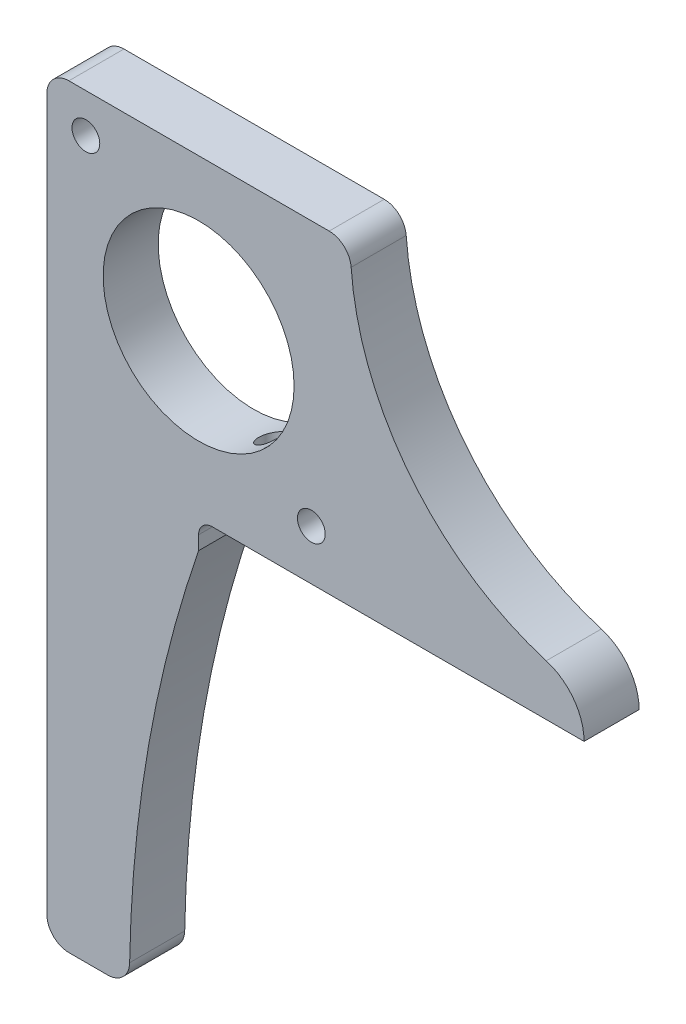
SolidWorks part; units mm, degrees
ref_plane "Front Plane" through (0, 0, 0) normal (0, 0, 1) x (1, 0, 0)
ref_plane "Top Plane" through (0, 0, 0) normal (0, 1, 0) x (1, 0, 0)
ref_plane "Right Plane" through (0, 0, 0) normal (1, 0, 0) x (0, 0, -1)
sketch "Sketch1" plane through (0, 0, 0) normal (0, 0, 1) x (1, 0, 0)
  line L0 (0, 0) -> (35, 0)
  line L1 (61.95, -36.27) -> (61.95, -43.3792) construction
  line L2 (9.525, -87.07) -> (0, -87.07)
  line L3 (0, -36.27) -> (0, 0)
  line L4 (30.5, -30.5) -> (4.5, -4.5) construction
  line L5 (4.5, -4.5) -> (30.5, -4.5) construction
  line L6 (4.5, -4.5) -> (4.5, -30.5) construction
  line L7 (4.5, -30.5) -> (30.5, -30.5) construction
  line L8 (30.5, -4.5) -> (30.5, -30.5) construction
  line L9 (0, -36.27) -> (35, -36.27) construction
  line L10 (35, -36.27) -> (35, 0) construction
  line L11 (4.5, -30.5) -> (30.5, -4.5) construction
  line L12 (9.525, -87.07) -> (9.525, -96.7126) construction
  line L13 (0, -87.07) -> (0, -36.27)
  line L14 (17.5, -36.27) -> (61.95, -36.27)
  line L15 (17.5, -36.27) -> (17.5, -39.445)
  line L16 (17.5, -39.445) -> (17.5, -17.5) construction
  arc A0 (9.525, -87.07) -> (17.5, -39.445) centre (155.7157, -87.07) cw
  arc A1 (35, 0) -> (57.5878, -30.3993) centre (66.75, 0) ccw
  circle A2 centre (4.5, -4.5) radius 1.6002
  circle A3 centre (17.5, -17.5) radius 11.0109
  circle A4 centre (30.5, -30.5) radius 1.6002
  arc A5 (61.95, -36.27) -> (57.5878, -30.3993) centre (55.8185, -36.27) ccw
  point P17 (17.5, -17.5)
  dimension "D3" = 3.2004
  dimension "D4" = 36.27
  dimension "D8" = 22.0218
  dimension "D9" = 31.75
  dimension "D2" = 26
  dimension "D5" = 35
  dimension "D6" = 50.8
  dimension "D7" = 9.525
  dimension "D10" = 3.175
  dimension "D11" = 44.45
extrude "Boss-Extrude1" add sketch "Sketch1" along normal blind 6.35
fillet "Fillet1" radius 2.54 4 edges at (0, 0, 3.175) (35, 0, 3.175) (9.525, -87.07, 3.175) (0, -87.07, 3.175)
hole_wizard "#6-32 Tapped Hole1" positions "Sketch4" profile "Sketch3" tap size "#6-32" standard "ANSI Inch"
sketch "Sketch4" plane through (0, -36.27, 0) normal (0, -1, 0) x (-1, 0, 0)
  line L0 (-17.5, -3.175) -> (-61.95, -3.175) construction
  line L3 (-17.5, -6.35) -> (-17.5, 0) construction
  line L4 (-61.95, -6.35) -> (-61.95, 0) construction
  point P0 (-22.58, -3.175)
  point P2 (-47.98, -3.175)
  dimension "D1" = 5.08
  dimension "D2" = 25.4
sketch "Sketch3" plane through (22.58, -36.27, 3.175) normal (1, 0, 0) x (0, 0, -1)
  line L0 (0, 0) -> (0, 10.2005)
  line L1 (0, 10.2005) -> (1.3525, 9.3878)
  line L2 (1.3525, 9.3878) -> (1.3525, 0)
  line L5 (1.3525, 0) -> (0, 0)
  line L10 (0, 10.2005) -> (-1.3526, 9.3878) construction
  line L11 (0, -6.35) -> (0, 107.95) construction
  dimension "Tap Drill Dia." = 2.7051
  dimension "Tap Drill Depth" = 9.3878
  dimension "Drill Angle" = 118
cosmetic thread "Hole Thread1" parameters "D1"=7.0104, "D2"=3.5052
cosmetic thread "Hole Thread2" parameters "D1"=7.0104, "D2"=3.5052
fillet "Fillet2" radius 1.5875 1 edges at (17.5, -36.27, 3.175)
